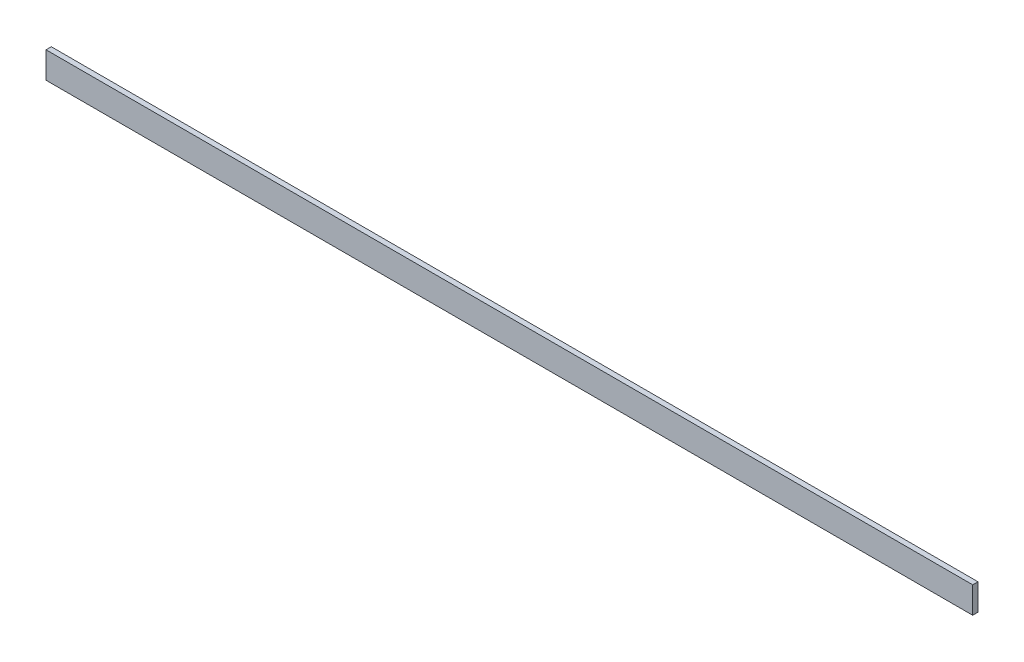
SolidWorks part; units mm, degrees
ref_plane "Front Plane" through (0, 0, 0) normal (0, 0, 1) x (1, 0, 0)
ref_plane "Top Plane" through (0, 0, 0) normal (0, 1, 0) x (1, 0, 0)
ref_plane "Right Plane" through (0, 0, 0) normal (1, 0, 0) x (0, 0, -1)
sketch "Sketch1" plane through (0, 0, 0) normal (0, 0, 1) x (1, 0, 0)
  line L0 (-177.1275, 4.721) -> (174.0444, 4.721)
  line L1 (-177.1275, 4.721) -> (-177.1275, -5.279)
  line L2 (-177.1275, -5.279) -> (174.0444, -5.279)
  line L3 (174.0444, 4.721) -> (174.0444, -5.279)
  dimension "D1" = 351.1719
  dimension "D2" = 10
extrude "Boss-Extrude1" add sketch "Sketch1" along normal blind 2
